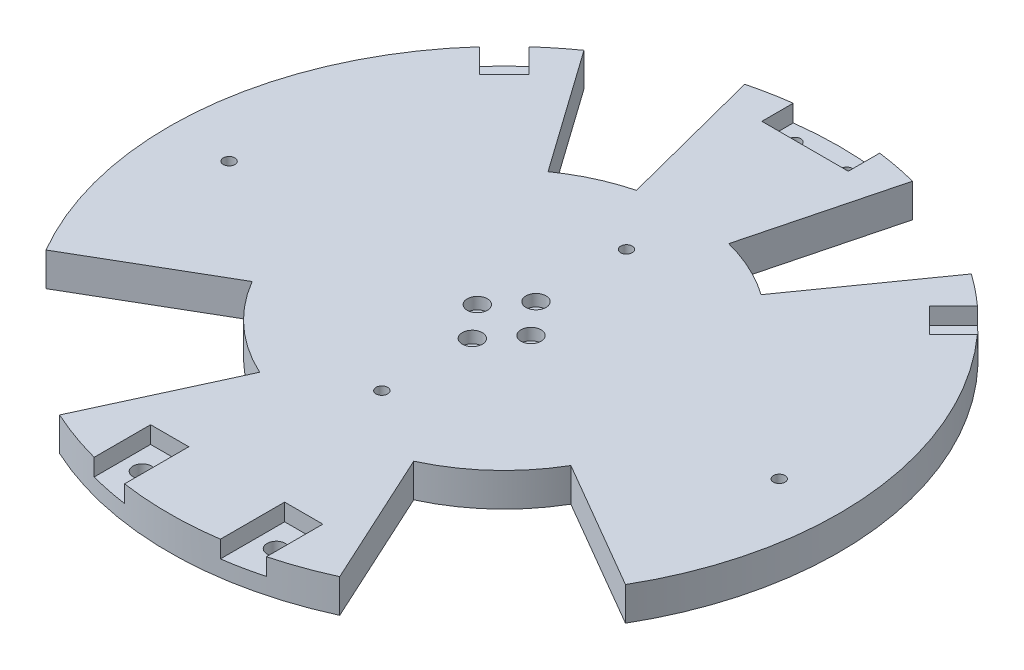
SolidWorks part; units mm, degrees
ref_plane "Front Plane" through (0, 0, 0) normal (0, 0, 1) x (1, 0, 0)
ref_plane "Top Plane" through (0, 0, 0) normal (0, 1, 0) x (1, 0, 0)
ref_plane "Right Plane" through (0, 0, 0) normal (1, 0, 0) x (0, 0, -1)
sketch "Sketch1" plane through (0, 0, 0) normal (0, 1, 0) x (1, 0, 0)
  circle A0 centre (0, 0) radius 100
  dimension "D1" = 200
extrude "Boss-Extrude1" add sketch "Sketch1" along normal blind 10
sketch "Sketch4" plane through (0, 10, 0) normal (0, 1, 0) x (1, 0, 0)
  circle A0 centre (-82.085, 0) radius 1.73
  circle A1 centre (0, -36.5) radius 1.73
  circle A2 centre (82.085, 0) radius 1.73
  circle A3 centre (0, 36.5) radius 1.73
  dimension "D1" = 3.46
  dimension "D2" = 3.46
  dimension "D3" = 3.46
  dimension "D4" = 3.46
extrude "Cut-Extrude2" cut sketch "Sketch4" against normal through all
sketch "Sketch6" plane through (0, 0, 0) normal (0, -1, 0) x (1, 0, 0)
  circle A0 centre (8, 0) radius 1.75
  circle A1 centre (0, 9.5) radius 1.75
  circle A2 centre (-8, 0) radius 1.75
  circle A3 centre (0, -9.5) radius 1.75
  dimension "D1" = 3.5
  dimension "D2" = 3.5
  dimension "D3" = 3.5
  dimension "D4" = 3.5
extrude "Cut-Extrude3" cut sketch "Sketch6" against normal up to surface (10 mm away) up to face at (-82.085, 10, 1.73)
sketch "Sketch7" plane through (0, 10, 0) normal (0, 1, 0) x (1, 0, 0)
  circle A0 centre (0, 9.5) radius 3
  circle A1 centre (-8, 0) radius 3
  circle A2 centre (0, -9.5) radius 3
  circle A3 centre (8, 0) radius 3
  dimension "D1" = 6
  dimension "D2" = 6
  dimension "D3" = 6
  dimension "D4" = 6
extrude "Cut-Extrude4" cut sketch "Sketch7" against normal offset from surface (3.5 mm away) 18.5
sketch "Sketch8" plane through (0, 10, 0) normal (0, 1, 0) x (1, 0, 0)
  line L4 (-14.5, -80) -> (-14.5, -142) construction
  line L5 (-25.5, -142) -> (-25.5, -80) construction
  line L6 (-25.5, -96.6941) -> (-25.5, -80) construction
  line L12 (-14.5, -80) -> (-14.5, -98.9432) construction
  line L13 (14.5, -98.9432) -> (14.5, -80) construction
  line L14 (25.5, -80) -> (25.5, -96.6941) construction
  line L15 (-14.5, -80) -> (-25.5, -80) construction
  line L16 (25.5, -80) -> (14.5, -80) construction
  line L17 (-14.3, -79.8) -> (-14.3, -99.1743)
  line L18 (-25.7, -96.8481) -> (-25.7, -79.8)
  line L19 (-14.3, -79.8) -> (-25.7, -79.8)
  line L20 (25.7, -79.8) -> (25.7, -96.8481)
  line L21 (14.3, -99.1743) -> (14.3, -79.8)
  line L22 (25.7, -79.8) -> (14.3, -79.8)
  line L23 (25.5, -80) -> (25.5, -142) construction
  line L24 (14.5, -142) -> (14.5, -80) construction
  arc A0 (-25.5, -96.6941) -> (-14.5, -98.9432) centre (0, 0) ccw construction
  circle A5 centre (0, 0) radius 100 construction
  arc A6 (14.5, -98.9432) -> (25.5, -96.6941) centre (0, 0) ccw construction
  arc A7 (-25.7, -96.8481) -> (-14.3, -99.1743) centre (0, 0) ccw
  arc A8 (14.3, -99.1743) -> (25.7, -96.8481) centre (0, 0) ccw
  dimension "D1" = 0.2
extrude "Cut-Extrude5" cut sketch "Sketch8" against normal blind 5.1
sketch "Sketch9" plane through (0, 10, 0) normal (0, 1, 0) x (1, 0, 0)
  line L0 (12.7, 90) -> (12.7, 154.6) construction
  line L1 (-12.7, 154.6) -> (-12.7, 90) construction
  line L2 (12.7, 90) -> (12.7, 98.9886) construction
  line L3 (-12.7, 98.9886) -> (-12.7, 90) construction
  line L4 (12.7, 90) -> (-12.7, 90) construction
  line L5 (-12.9, 99.1645) -> (-12.9, 89.8)
  line L6 (12.9, 89.8) -> (-12.9, 89.8)
  line L7 (12.9, 89.8) -> (12.9, 99.1645)
  arc A1 (12.7, 98.9886) -> (-12.7, 98.9886) centre (0, 0) ccw construction
  arc A2 (12.9, 99.1645) -> (-12.9, 99.1645) centre (0, 0) ccw
  arc A3 (25.7, -96.6411) -> (-25.7, -96.6411) centre (0, 0) ccw construction
  dimension "D1" = 0.2
extrude "Cut-Extrude6" cut sketch "Sketch9" against normal blind 5.1
sketch "Sketch10" plane through (0, 4.9, 0) normal (0, 1, 0) x (1, 0, 0)
  circle A0 centre (-7.7, 94.4822) radius 1.75
  circle A1 centre (7.7, 94.4822) radius 1.75
  dimension "D1" = 3.5
  dimension "D2" = 3.5
extrude "Cut-Extrude7" cut sketch "Sketch10" against normal through all
sketch "Sketch12" plane through (0, 10, 0) normal (0, 1, 0) x (1, 0, 0)
  line L0 (67.1751, 60.1041) -> (107.4803, 100.4092) construction
  line L1 (100.4092, 107.4803) -> (60.1041, 67.1751) construction
  line L2 (67.1751, 60.1041) -> (74.1578, 67.0867) construction
  line L3 (67.0867, 74.1578) -> (60.1041, 67.1751) construction
  line L4 (67.1751, 60.1041) -> (60.1041, 67.1751) construction
  line L5 (67.0797, 74.4336) -> (59.8212, 67.1751)
  line L6 (67.1751, 59.8212) -> (59.8212, 67.1751)
  line L7 (67.1751, 59.8212) -> (74.4336, 67.0797)
  arc A0 (25.7, -96.6411) -> (12.9, 99.1645) centre (0, 0) ccw construction
  arc A1 (74.1578, 67.0867) -> (67.0867, 74.1578) centre (0, 0) ccw construction
  arc A2 (74.4336, 67.0797) -> (67.0797, 74.4336) centre (0, 0) ccw
  dimension "D1" = 0.2
extrude "Cut-Extrude9" cut sketch "Sketch12" against normal blind 5.1
sketch "Sketch13" plane through (0, 4.9, 0) normal (0, 1, 0) x (1, 0, 0)
  circle A0 centre (67.1751, 67.1751) radius 1.75
  dimension "D1" = 3.5
extrude "Cut-Extrude10" cut sketch "Sketch13" against normal through all
sketch "Sketch14" plane through (0, 10, 0) normal (0, 1, 0) x (1, 0, 0)
  line L0 (0, 0) -> (0, 100) construction
  arc A0 (12.9, 99.1645) -> (-12.9, 99.1645) centre (0, 0) ccw construction
ref_plane "Plane1" through (0, 0, 0) normal (1, 0, 0) x (0, 0, -1)
mirror "Mirror1" about plane through (0, 0, 0) normal (1, 0, 0) of "Cut-Extrude10", "Cut-Extrude9"
sketch "Sketch15" plane through (0, 10, 0) normal (0, 1, 0) x (1, 0, 0)
  line L0 (0, 0) -> (0, 78.7078) construction
  line L1 (-47.5503, -27.64) -> (0, 0) construction
  line L2 (-22.9844, -49.9672) -> (-41.7898, -90.8494)
  line L3 (-47.5503, -27.64) -> (-86.4551, -50.2545)
  line L4 (-22.9844, -49.9672) -> (0, 0) construction
  line L5 (-82.5, -27.64) -> (-5, -27.64) construction
  line L6 (22.9844, -49.9672) -> (41.7898, -90.8494)
  line L7 (47.5503, -27.64) -> (86.4551, -50.2545)
  arc A0 (-47.5503, -27.64) -> (-22.9844, -49.9672) centre (0, 0) ccw
  arc A2 (-74.292, 66.9381) -> (-25.7, -96.6411) centre (0, 0) ccw construction
  arc A3 (-86.4551, -50.2545) -> (-41.7898, -90.8494) centre (0, 0) ccw
  arc A4 (47.5503, -27.64) -> (22.9844, -49.9672) centre (0, 0) cw
  arc A5 (86.4551, -50.2545) -> (41.7898, -90.8494) centre (0, 0) cw
  dimension "D1" = 110
  dimension "D2" = 10
extrude "Cut-Extrude11" cut sketch "Sketch15" against normal through all
sketch "Sketch17" plane through (0, 10, 0) normal (0, 1, 0) x (1, 0, 0)
  line L0 (-31.7845, 44.8859) -> (-57.79, 81.6107)
  line L1 (-13.7738, 53.2474) -> (-25.0433, 96.8134)
  line L2 (0, 0) -> (0, 113.7097) construction
  line L3 (-31.7845, 44.8859) -> (0, 0) construction
  line L4 (-13.7738, 53.2474) -> (0, 0) construction
  line L5 (13.7738, 53.2474) -> (25.0433, 96.8134)
  line L6 (31.7845, 44.8859) -> (57.79, 81.6107)
  arc A0 (-13.7738, 53.2474) -> (-31.7845, 44.8859) centre (0, 0) ccw
  arc A1 (-12.9, 99.1645) -> (-66.9381, 74.292) centre (0, 0) ccw construction
  arc A2 (-25.0433, 96.8134) -> (-57.79, 81.6107) centre (0, 0) ccw
  arc A3 (13.7738, 53.2474) -> (31.7845, 44.8859) centre (0, 0) cw
  arc A4 (25.0433, 96.8134) -> (57.79, 81.6107) centre (0, 0) cw
  dimension "D1" = 10
  dimension "D2" = 10
extrude "Cut-Extrude12" cut sketch "Sketch17" against normal through all
sketch "Sketch18" plane through (0, 4.9, 0) normal (0, 1, 0) x (1, 0, 0)
  circle A0 centre (-20, -88) radius 2.75
  circle A1 centre (20, -88) radius 2.75
  dimension "D1" = 5.5
  dimension "D2" = 5.5
extrude "Cut-Extrude13" cut sketch "Sketch18" against normal through all
